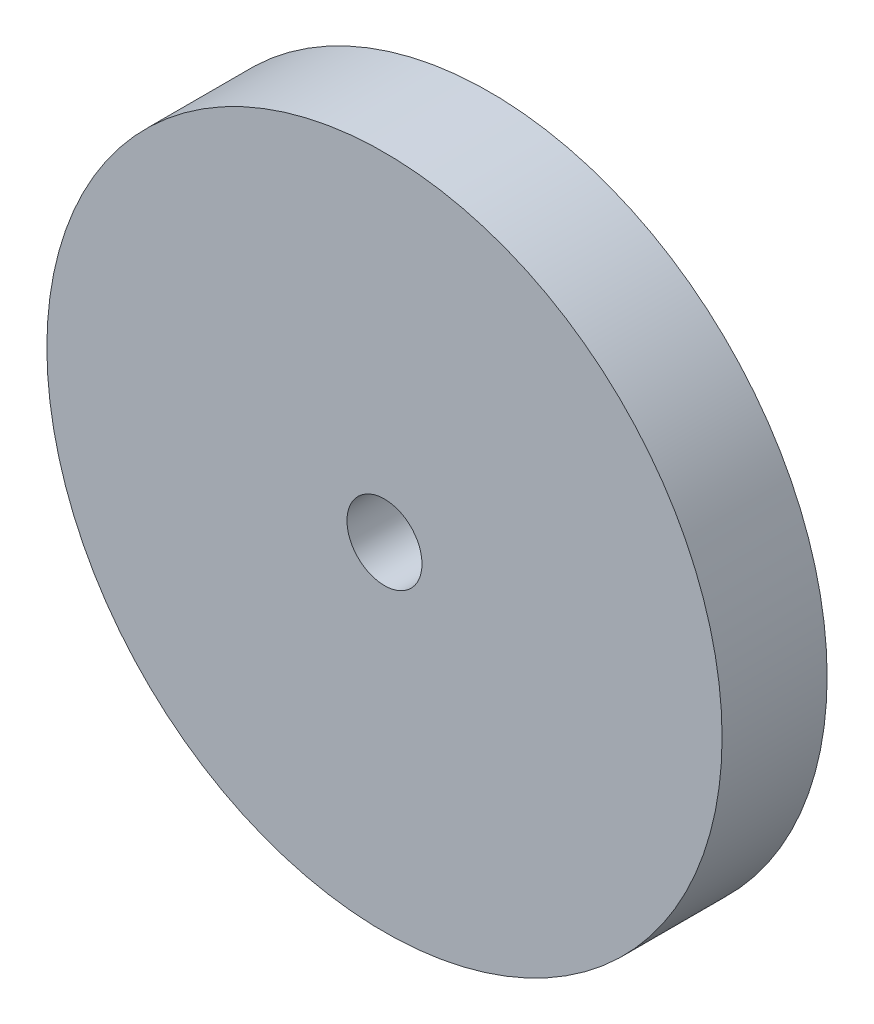
SolidWorks part; units mm, degrees
ref_plane "前基準面" through (0, 0, 0) normal (0, 0, 1) x (1, 0, 0)
ref_plane "上基準面" through (0, 0, 0) normal (0, 1, 0) x (1, 0, 0)
ref_plane "右基準面" through (0, 0, 0) normal (1, 0, 0) x (0, 0, -1)
sketch "草圖1" plane through (0, 0, 0) normal (0, 0, 1) x (1, 0, 0)
  circle A0 centre (0, 0) radius 9
  circle A1 centre (0, 0) radius 1
  dimension "D1" = 18
  dimension "D2" = 2
extrude "填料-伸長1" add sketch "草圖1" along normal blind 2.8
